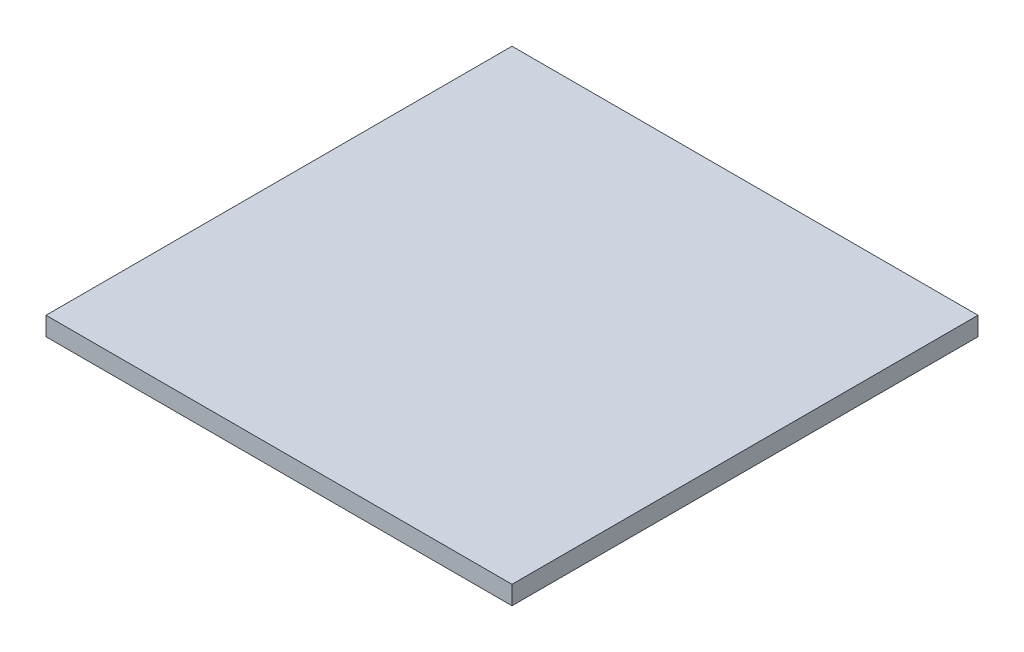
SolidWorks part; units mm, degrees
material "paste"
ref_plane "Front Plane" through (0, 0, 0) normal (0, 0, 1) x (1, 0, 0)
ref_plane "Top Plane" through (0, 0, 0) normal (0, 1, 0) x (1, 0, 0)
ref_plane "Right Plane" through (0, 0, 0) normal (1, 0, 0) x (0, 0, -1)
sketch "Sketch1" plane through (0, 0, 0) normal (0, 1, 0) x (1, 0, 0)
  line L1 (-20.91, 16.2319) -> (4.09, 16.2319)
  line L2 (-20.91, 16.2319) -> (-20.91, -8.7681)
  line L3 (-20.91, -8.7681) -> (4.09, -8.7681)
  line L4 (4.09, 16.2319) -> (4.09, -8.7681)
  dimension "D1" = 25
  dimension "D2" = 25
sketch "Sketch2" plane through (0, 0, 0) normal (0, 1, 0) x (1, 0, 0)
  line L0 (-20.91, 16.2319) -> (4.09, 16.2319)
  line L1 (-20.91, 16.2319) -> (-20.91, -8.7681)
  line L2 (-20.91, -8.7681) -> (4.09, -8.7681)
  line L3 (4.09, 16.2319) -> (4.09, -8.7681)
extrude "Boss-Extrude1" add sketch "Sketch2" along normal blind 1
